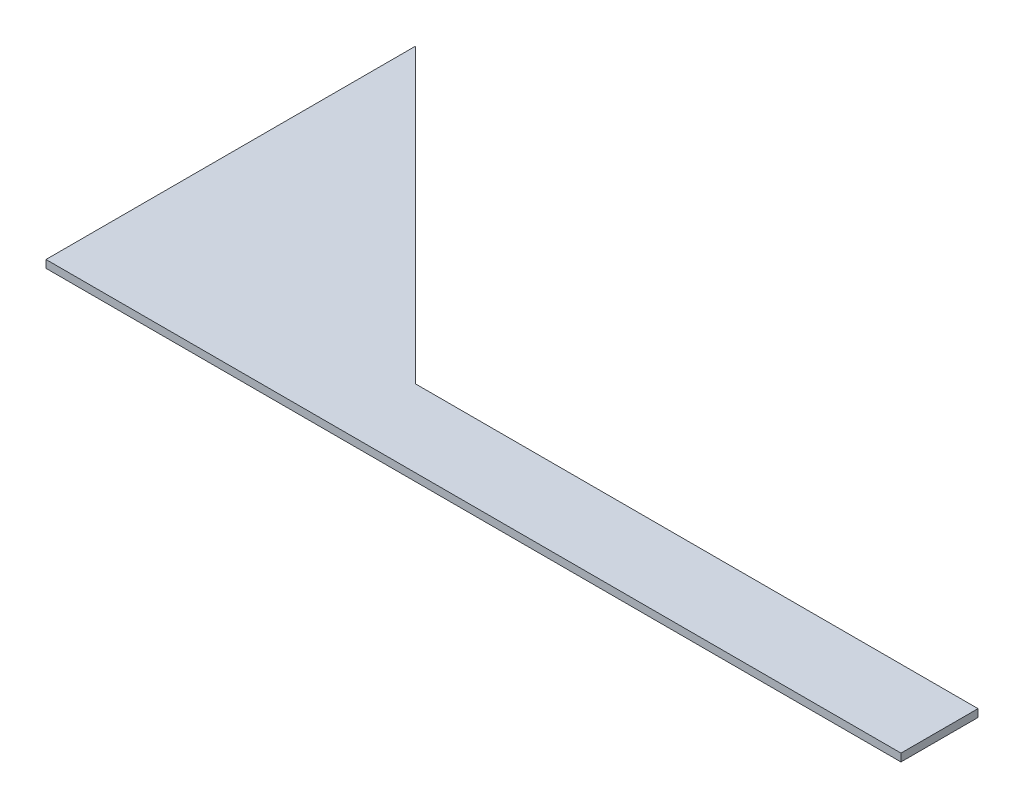
SolidWorks part; units mm, degrees
material "ASTM A36 Steel"
ref_plane "Front Plane" through (0, 0, 0) normal (0, 0, 1) x (1, 0, 0)
ref_plane "Top Plane" through (0, 0, 0) normal (0, 1, 0) x (1, 0, 0)
ref_plane "Right Plane" through (0, 0, 0) normal (1, 0, 0) x (0, 0, -1)
sketch "Sketch1" plane through (0, 0, 0) normal (0, 1, 0) x (1, 0, 0)
  line L0 (0, 0) -> (0, 152.4)
  line L1 (0, 152.4) -> (152.4, 0)
  line L2 (152.4, 0) -> (0, 0)
  line L3 (120.65, 31.75) -> (352.425, 31.75)
  line L4 (352.425, 31.75) -> (352.425, 0)
  line L5 (352.425, 0) -> (152.4, 0)
  dimension "D1" = 152.4
  dimension "D2" = 152.4
  dimension "D3" = 352.425
  dimension "D4" = 31.75
extrude "Boss-Extrude1" add sketch "Sketch1" along normal blind 3.175 contours L2 L1 L0 | L5 L4 L3 L1
